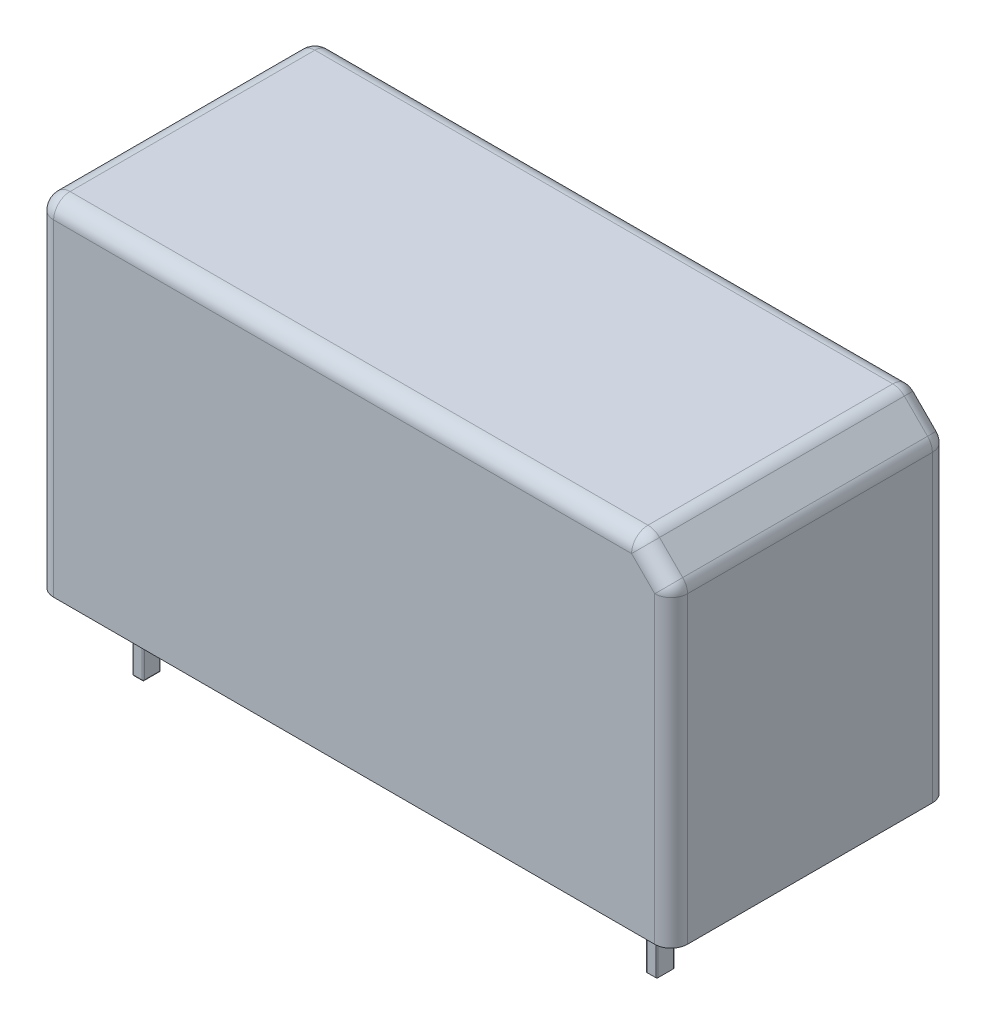
SolidWorks part; units mm, degrees
ref_plane "Спереди" through (0, 0, 0) normal (0, 0, 1) x (1, 0, 0)
ref_plane "Сверху" through (0, 0, 0) normal (0, 1, 0) x (1, 0, 0)
ref_plane "Справа" through (0, 0, 0) normal (1, 0, 0) x (0, 0, -1)
sketch "Эскиз1" plane through (0, 0, 0) normal (0, 1, 0) x (1, 0, 0)
  line L1 (-14.5, -6.35) -> (14.5, -6.35)
  line L2 (-14.5, -6.35) -> (-14.5, 6.35)
  line L3 (-14.5, 6.35) -> (14.5, 6.35)
  line L4 (14.5, -6.35) -> (14.5, 6.35)
  line L5 (-14.5, -6.35) -> (14.5, 6.35) construction
  line L6 (-14.5, 6.35) -> (14.5, -6.35) construction
  point P0 (0, 0)
  dimension "D1" = 29
  dimension "D2" = 12.7
extrude "Бобышка-Вытянуть1" add sketch "Эскиз1" along normal blind 15.7
sketch "Эскиз2" plane through (0, 0, 0) normal (0, -1, 0) x (1, 0, 0)
  line L0 (-14.5, -6.35) -> (-14.5, 6.35) construction
  line L1 (-12.3, 4.15) -> (-11.9, 4.15)
  line L2 (-12.35, 4.1) -> (-12.35, 3.4)
  line L3 (-12.3, 3.35) -> (-11.9, 3.35)
  line L4 (-11.85, 4.1) -> (-11.85, 3.4)
  line L5 (-12.35, 4.15) -> (-11.85, 3.35) construction
  line L6 (-12.35, 3.35) -> (-11.85, 4.15) construction
  line L7 (-7.35, 4.1) -> (-7.35, 3.4) [skipped]
  line L8 (-6.85, 4.1) -> (-6.85, 3.4) [skipped]
  line L9 (-7.3, 4.15) -> (-6.9, 4.15) [skipped]
  line L10 (-7.3, 3.35) -> (-6.9, 3.35) [skipped]
  line L11 (-2.35, 4.1) -> (-2.35, 3.4) [skipped]
  line L12 (-1.85, 4.1) -> (-1.85, 3.4) [skipped]
  line L13 (-2.3, 4.15) -> (-1.9, 4.15) [skipped]
  line L14 (-2.3, 3.35) -> (-1.9, 3.35) [skipped]
  line L27 (-7.35, -3.4) -> (-7.35, -4.1) [skipped]
  line L28 (-6.85, -3.4) -> (-6.85, -4.1) [skipped]
  line L29 (-7.3, -3.35) -> (-6.9, -3.35) [skipped]
  line L30 (-7.3, -4.15) -> (-6.9, -4.15) [skipped]
  line L31 (-2.35, -3.4) -> (-2.35, -4.1) [skipped]
  line L32 (-1.85, -3.4) -> (-1.85, -4.1) [skipped]
  line L33 (-2.3, -3.35) -> (-1.9, -3.35) [skipped]
  line L34 (-2.3, -4.15) -> (-1.9, -4.15) [skipped]
  line L39 (7.65, -3.4) -> (7.65, -4.1)
  line L40 (8.15, -3.4) -> (8.15, -4.1)
  line L41 (7.7, -3.35) -> (8.1, -3.35)
  line L42 (7.7, -4.15) -> (8.1, -4.15)
  line L47 (-12.35, -3.4) -> (-12.35, -4.1)
  line L48 (-11.85, -3.4) -> (-11.85, -4.1)
  line L49 (-12.3, -3.35) -> (-11.9, -3.35)
  line L50 (-12.3, -4.15) -> (-11.9, -4.15)
  line L51 (2.65, 4.1) -> (2.65, 3.4) [skipped]
  line L52 (3.15, 4.1) -> (3.15, 3.4) [skipped]
  line L53 (2.7, 4.15) -> (3.1, 4.15) [skipped]
  line L54 (2.7, 3.35) -> (3.1, 3.35) [skipped]
  line L55 (12.65, 4.1) -> (12.65, 3.4) [skipped]
  line L56 (13.15, 4.1) -> (13.15, 3.4) [skipped]
  line L57 (12.7, 4.15) -> (13.1, 4.15) [skipped]
  line L58 (12.7, 3.35) -> (13.1, 3.35) [skipped]
  line L59 (2.65, -3.4) -> (2.65, -4.1) [skipped]
  line L60 (3.15, -3.4) -> (3.15, -4.1) [skipped]
  line L61 (2.7, -3.35) -> (3.1, -3.35) [skipped]
  line L62 (2.7, -4.15) -> (3.1, -4.15) [skipped]
  line L63 (7.65, 4.1) -> (7.65, 3.4) [skipped]
  line L64 (8.15, 4.1) -> (8.15, 3.4) [skipped]
  line L65 (7.7, 4.15) -> (8.1, 4.15) [skipped]
  line L66 (7.7, 3.35) -> (8.1, 3.35) [skipped]
  line L67 (12.65, -3.4) -> (12.65, -4.1) [skipped]
  line L68 (13.15, -3.4) -> (13.15, -4.1) [skipped]
  line L69 (12.7, -3.35) -> (13.1, -3.35) [skipped]
  line L70 (12.7, -4.15) -> (13.1, -4.15) [skipped]
  line L71 (11.15, 4.15) -> (11.65, 3.35) construction
  line L72 (11.2, 4.15) -> (11.6, 4.15)
  line L73 (11.15, 3.35) -> (11.65, 4.15) construction
  line L74 (11.15, 4.1) -> (11.15, 3.4)
  line L75 (11.65, 4.1) -> (11.65, 3.4)
  line L76 (11.2, 3.35) -> (11.6, 3.35)
  line L83 (-12.1, 3.75) -> (12.9, 3.75) construction
  arc A0 (-12.35, 3.4) -> (-12.3, 3.35) centre (-12.3, 3.4) ccw
  arc A1 (-11.9, 3.35) -> (-11.85, 3.4) centre (-11.9, 3.4) ccw
  arc A2 (-11.9, 4.15) -> (-11.85, 4.1) centre (-11.9, 4.1) cw
  arc A3 (-12.3, 4.15) -> (-12.35, 4.1) centre (-12.3, 4.1) ccw
  arc A4 (-7.35, 3.4) -> (-7.3, 3.35) centre (-7.3, 3.4) ccw [skipped]
  arc A5 (-6.9, 3.35) -> (-6.85, 3.4) centre (-6.9, 3.4) ccw [skipped]
  arc A6 (-6.9, 4.15) -> (-6.85, 4.1) centre (-6.9, 4.1) cw [skipped]
  arc A7 (-7.3, 4.15) -> (-7.35, 4.1) centre (-7.3, 4.1) ccw [skipped]
  arc A8 (-2.35, 3.4) -> (-2.3, 3.35) centre (-2.3, 3.4) ccw [skipped]
  arc A9 (-1.9, 3.35) -> (-1.85, 3.4) centre (-1.9, 3.4) ccw [skipped]
  arc A10 (-1.9, 4.15) -> (-1.85, 4.1) centre (-1.9, 4.1) cw [skipped]
  arc A11 (-2.3, 4.15) -> (-2.35, 4.1) centre (-2.3, 4.1) ccw [skipped]
  arc A24 (-7.35, -4.1) -> (-7.3, -4.15) centre (-7.3, -4.1) ccw [skipped]
  arc A25 (-6.9, -4.15) -> (-6.85, -4.1) centre (-6.9, -4.1) ccw [skipped]
  arc A26 (-6.9, -3.35) -> (-6.85, -3.4) centre (-6.9, -3.4) cw [skipped]
  arc A27 (-7.3, -3.35) -> (-7.35, -3.4) centre (-7.3, -3.4) ccw [skipped]
  arc A28 (-2.35, -4.1) -> (-2.3, -4.15) centre (-2.3, -4.1) ccw [skipped]
  arc A29 (-1.9, -4.15) -> (-1.85, -4.1) centre (-1.9, -4.1) ccw [skipped]
  arc A30 (-1.9, -3.35) -> (-1.85, -3.4) centre (-1.9, -3.4) cw [skipped]
  arc A31 (-2.3, -3.35) -> (-2.35, -3.4) centre (-2.3, -3.4) ccw [skipped]
  arc A36 (7.65, -4.1) -> (7.7, -4.15) centre (7.7, -4.1) ccw
  arc A37 (8.1, -4.15) -> (8.15, -4.1) centre (8.1, -4.1) ccw
  arc A38 (8.1, -3.35) -> (8.15, -3.4) centre (8.1, -3.4) cw
  arc A39 (7.7, -3.35) -> (7.65, -3.4) centre (7.7, -3.4) ccw
  arc A44 (-12.35, -4.1) -> (-12.3, -4.15) centre (-12.3, -4.1) ccw
  arc A45 (-11.9, -4.15) -> (-11.85, -4.1) centre (-11.9, -4.1) ccw
  arc A46 (-11.9, -3.35) -> (-11.85, -3.4) centre (-11.9, -3.4) cw
  arc A47 (-12.3, -3.35) -> (-12.35, -3.4) centre (-12.3, -3.4) ccw
  arc A48 (2.65, 3.4) -> (2.7, 3.35) centre (2.7, 3.4) ccw [skipped]
  arc A49 (3.1, 3.35) -> (3.15, 3.4) centre (3.1, 3.4) ccw [skipped]
  arc A50 (3.1, 4.15) -> (3.15, 4.1) centre (3.1, 4.1) cw [skipped]
  arc A51 (2.7, 4.15) -> (2.65, 4.1) centre (2.7, 4.1) ccw [skipped]
  arc A52 (12.65, 3.4) -> (12.7, 3.35) centre (12.7, 3.4) ccw [skipped]
  arc A53 (13.1, 3.35) -> (13.15, 3.4) centre (13.1, 3.4) ccw [skipped]
  arc A54 (13.1, 4.15) -> (13.15, 4.1) centre (13.1, 4.1) cw [skipped]
  arc A55 (12.7, 4.15) -> (12.65, 4.1) centre (12.7, 4.1) ccw [skipped]
  arc A56 (2.65, -4.1) -> (2.7, -4.15) centre (2.7, -4.1) ccw [skipped]
  arc A57 (3.1, -4.15) -> (3.15, -4.1) centre (3.1, -4.1) ccw [skipped]
  arc A58 (3.1, -3.35) -> (3.15, -3.4) centre (3.1, -3.4) cw [skipped]
  arc A59 (2.7, -3.35) -> (2.65, -3.4) centre (2.7, -3.4) ccw [skipped]
  arc A60 (12.7, -3.35) -> (12.65, -3.4) centre (12.7, -3.4) ccw [skipped]
  arc A61 (7.65, 3.4) -> (7.7, 3.35) centre (7.7, 3.4) ccw [skipped]
  arc A62 (8.1, 3.35) -> (8.15, 3.4) centre (8.1, 3.4) ccw [skipped]
  arc A63 (8.1, 4.15) -> (8.15, 4.1) centre (8.1, 4.1) cw [skipped]
  arc A64 (7.7, 4.15) -> (7.65, 4.1) centre (7.7, 4.1) ccw [skipped]
  arc A65 (12.65, -4.1) -> (12.7, -4.15) centre (12.7, -4.1) ccw [skipped]
  arc A66 (13.1, -4.15) -> (13.15, -4.1) centre (13.1, -4.1) ccw [skipped]
  arc A67 (13.1, -3.35) -> (13.15, -3.4) centre (13.1, -3.4) cw [skipped]
  arc A68 (11.6, 3.35) -> (11.65, 3.4) centre (11.6, 3.4) ccw
  arc A69 (11.15, 3.4) -> (11.2, 3.35) centre (11.2, 3.4) ccw
  arc A70 (11.2, 4.15) -> (11.15, 4.1) centre (11.2, 4.1) ccw
  arc A71 (11.6, 4.15) -> (11.65, 4.1) centre (11.6, 4.1) cw
  point P0 (-12.1, 3.75)
  point P8 (-14.5, 0)
  point P21 (-11.85, 3.75)
  point P22 (11.4, 3.75)
  point P63 (11.65, 3.75)
  point P110 (11.15, 3.75)
  dimension "D1" = 0.05
  dimension "D2" = 0.5
  dimension "D3" = 3.75
  dimension "D4" = 2.4
  dimension "D5" = 0.8
  dimension "D8" = 0.8
  dimension "D11" = 0.5
  dimension "D6" = 6
  dimension "D7" = 2
extrude "Бобышка-Вытянуть2" add sketch "Эскиз2" along normal blind 3.5
fillet "Скругление1" radius 0.05 24 edges at (-11.8646, -3.5, 3.3646) (-12.1, -3.5, 3.35) (-12.3354, -3.5, 3.3646) (-12.35, -3.5, 3.75) (-12.3354, -3.5, 4.1354) (-12.1, -3.5, 4.15) (-11.8646, -3.5, 4.1354) (-11.8646, -3.5, -4.1354) (-12.1, -3.5, -4.15) (-12.3354, -3.5, -4.1354) (-12.35, -3.5, -3.75) (-12.3354, -3.5, -3.3646) (-12.1, -3.5, -3.35) (-11.8646, -3.5, -3.3646) (8.1354, -3.5, -4.1354) (7.9, -3.5, -4.15) (7.6646, -3.5, -4.1354) (7.65, -3.5, -3.75) (7.6646, -3.5, -3.3646) (7.9, -3.5, -3.35) (8.1354, -3.5, -3.3646) (-11.85, -3.5, 3.75) (-11.85, -3.5, -3.75) (8.15, -3.5, -3.75)
chamfer "Фаска1" distance 1.5 angle 45 1 edges at (14.5, 15.7, 0)
fillet "Скругление2" radius 0.75 11 edges at (13.75, 14.95, -6.35) (-14.5, 7.85, 6.35) (-14.5, 7.85, -6.35) (14.5, 7.1, -6.35) (14.5, 7.1, 6.35) (13.75, 14.95, 6.35) (14.5, 14.2, 0) (13, 15.7, 0) (-0.75, 15.7, -6.35) (-14.5, 15.7, 0) (-0.75, 15.7, 6.35)
